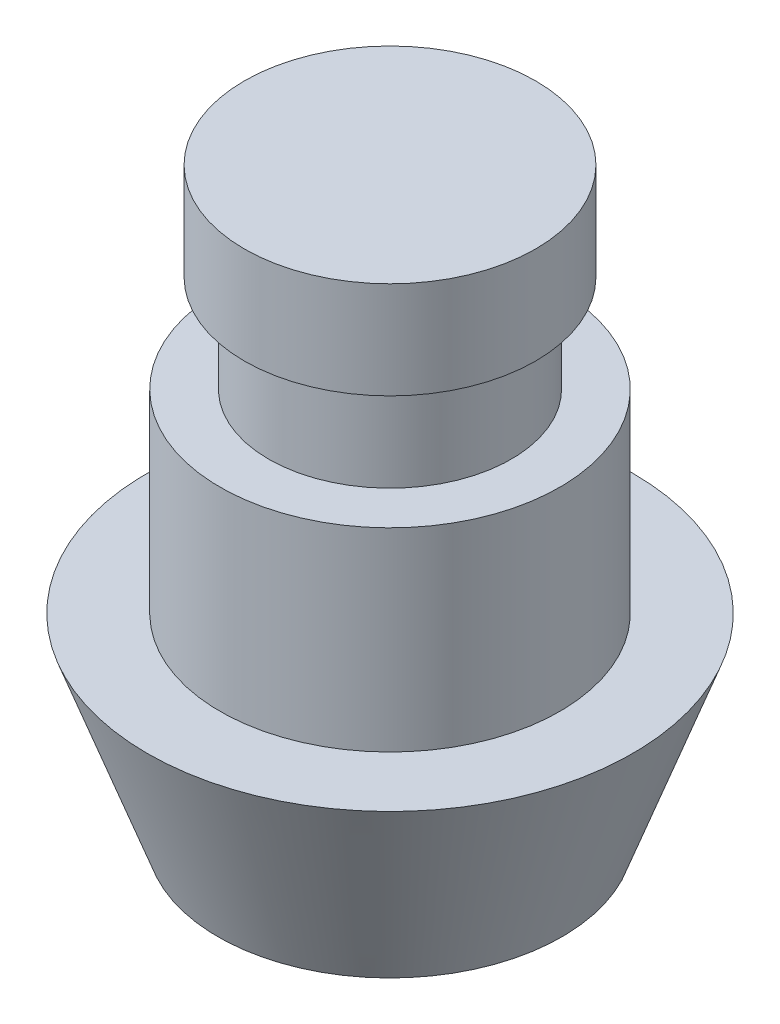
SolidWorks part; units mm, degrees
ref_plane "Front Plane" through (0, 0, 0) normal (0, 0, 1) x (1, 0, 0)
ref_plane "Top Plane" through (0, 0, 0) normal (0, 1, 0) x (1, 0, 0)
ref_plane "Right Plane" through (0, 0, 0) normal (1, 0, 0) x (0, 0, -1)
sketch "Sketch1" plane through (0, 0, 0) normal (0, 1, 0) x (1, 0, 0)
  circle A0 centre (0, 0) radius 3
  dimension "D1" = 6
extrude "Boss-Extrude1" add sketch "Sketch1" along normal blind 2
sketch "Sketch2" plane through (0, 0, 0) normal (0, -1, 0) x (1, 0, 0)
  circle A0 centre (0, 0) radius 2.5
  circle A1 centre (0, 0) radius 3
  circle A2 centre (0, 0) radius 3
  dimension "D2" = 5
  dimension "D1" = 0
extrude "Boss-Extrude2" add sketch "Sketch2" along normal blind 2 contours A0
sketch "Sketch3" plane through (0, -2, 0) normal (0, -1, 0) x (1, 0, 0)
  circle A0 centre (0, 0) radius 3.5
  dimension "D1" = 7
extrude "Boss-Extrude3" add sketch "Sketch3" along normal blind 4
sketch "Sketch4" plane through (0, -6, 0) normal (0, -1, 0) x (1, 0, 0)
  circle A0 centre (0, 0) radius 5
  dimension "D1" = 10
extrude "Boss-Extrude4" add sketch "Sketch4" along normal blind 4 draft 20
